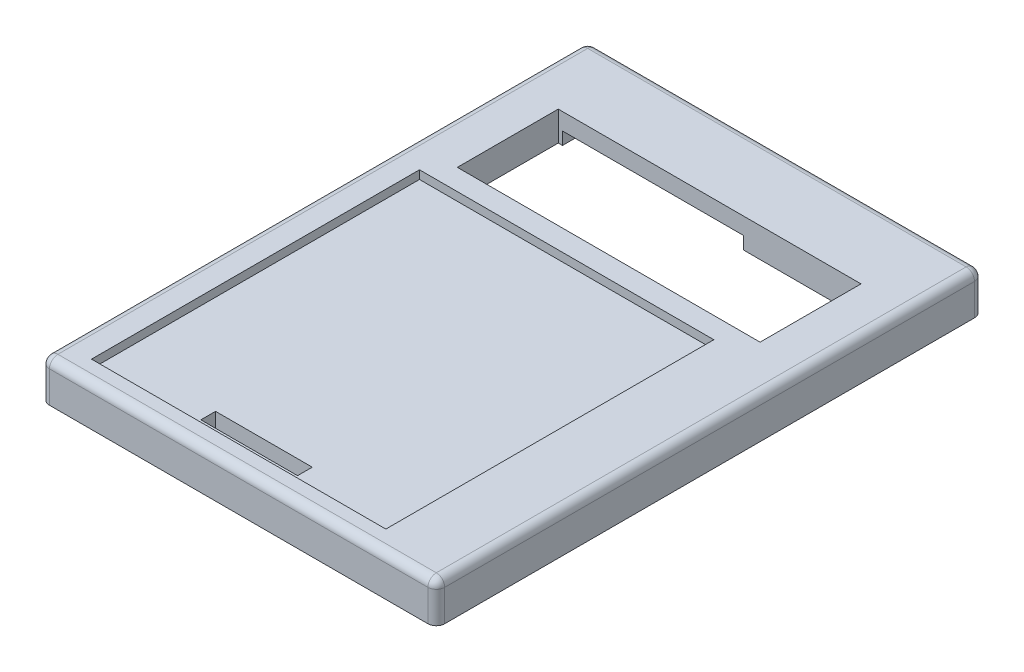
SolidWorks part; units mm, degrees
ref_plane "Front Plane" through (0, 0, 0) normal (0, 0, 1) x (1, 0, 0)
ref_plane "Top Plane" through (0, 0, 0) normal (0, 1, 0) x (1, 0, 0)
ref_plane "Right Plane" through (0, 0, 0) normal (1, 0, 0) x (0, 0, -1)
sketch "Sketch1" plane through (0, 0, 0) normal (0, 1, 0) x (1, 0, 0)
  line L1 (0, 0) -> (94, 0)
  line L2 (0, 0) -> (0, 130)
  line L3 (0, 130) -> (94, 130)
  line L4 (94, 0) -> (94, 130)
  dimension "D1" = 130
  dimension "D2" = 94
extrude "Boss-Extrude1" add sketch "Sketch1" along normal blind 7
sketch "Sketch2" plane through (0, 7, 0) normal (0, 1, 0) x (1, 0, 0)
  line L0 (94, 130) -> (0, 130) construction
  line L1 (11, 112) -> (83, 112)
  line L2 (11, 112) -> (11, 88)
  line L3 (11, 88) -> (83, 88)
  line L4 (83, 112) -> (83, 88)
  point P6 (47, 112)
  point P7 (47, 130)
  dimension "D1" = 72
  dimension "D2" = 24
  dimension "D3" = 18
extrude "Cut-Extrude1" cut sketch "Sketch2" against normal through all
sketch "Sketch3" plane through (0, 0, 0) normal (0, -1, 0) x (1, 0, 0)
  line L0 (83, -88) -> (83, -112) construction
  line L1 (89, -109) -> (83, -109)
  line L2 (89, -109) -> (89, -91)
  line L3 (89, -91) -> (83, -91)
  line L4 (83, -109) -> (83, -91)
  point P4 (83, -100)
  point P7 (83, -100)
  dimension "D1" = 6
  dimension "D2" = 18
extrude "Cut-Extrude2" cut sketch "Sketch3" against normal blind 3.5
sketch "Sketch4" plane through (0, 0, 0) normal (0, -1, 0) x (1, 0, 0)
  line L1 (55, -119.5) -> (12, -119.5)
  line L2 (55, -119.5) -> (55, -112)
  line L3 (55, -112) -> (12, -112)
  line L4 (12, -119.5) -> (12, -112)
  line L5 (83, -112) -> (11, -112) construction
  line L6 (0, -130) -> (0, 0) construction
  dimension "D1" = 43
  dimension "D2" = 7.5
  dimension "D3" = 12
extrude "Cut-Extrude3" cut sketch "Sketch4" against normal blind 3
sketch "Sketch5" plane through (0, 7, 0) normal (0, 1, 0) x (1, 0, 0)
  line L0 (0, 0) -> (94, 0) construction
  line L1 (7, 83) -> (77, 83)
  line L2 (7, 83) -> (7, 5)
  line L3 (7, 5) -> (77, 5)
  line L4 (77, 83) -> (77, 5)
  line L5 (0, 130) -> (0, 0) construction
  dimension "D1" = 78
  dimension "D2" = 70
  dimension "D3" = 5
  dimension "D4" = 7
extrude "Cut-Extrude4" cut sketch "Sketch5" against normal blind 2
sketch "Sketch6" plane through (0, 5, 0) normal (0, 1, 0) x (1, 0, 0)
  line L0 (7, 5) -> (77, 5) construction
  line L1 (30.5, 11) -> (53.5, 11)
  line L2 (30.5, 11) -> (30.5, 7.5)
  line L3 (30.5, 7.5) -> (53.5, 7.5)
  line L4 (53.5, 11) -> (53.5, 7.5)
  point P6 (42, 7.5)
  point P7 (42, 5)
  dimension "D1" = 23
  dimension "D2" = 3.5
  dimension "D3" = 2.5
extrude "Cut-Extrude5" cut sketch "Sketch6" against normal through all
fillet "Fillet1" radius 2 8 edges at (94, 3.5, -130) (0, 3.5, -130) (0, 3.5, 0) (94, 3.5, 0) (47, 7, 0) (94, 7, -65) (47, 7, -130) (0, 7, -65)
sketch "Sketch8" plane through (0, 0, 0) normal (0, -1, 0) x (1, 0, 0)
  line L0 (92, -130) -> (2, -130) construction
  line L1 (92.25, -128.25) -> (1.75, -128.25)
  line L2 (92.25, -128.25) -> (92.25, -1.75)
  line L3 (92.25, -1.75) -> (1.75, -1.75)
  line L4 (1.75, -128.25) -> (1.75, -1.75)
  line L5 (0, -128) -> (0, -2) construction
  line L6 (2, 0) -> (92, 0) construction
  line L7 (94, -2) -> (94, -128) construction
  line L8 (92, -130) -> (2, -130)
  line L9 (94, -2) -> (94, -128)
  line L10 (2, 0) -> (92, 0)
  line L11 (0, -128) -> (0, -2)
  arc A0 (0, -128) -> (2, -130) centre (2, -128) ccw construction
  arc A1 (92, -130) -> (94, -128) centre (92, -128) ccw construction
  arc A2 (94, -2) -> (92, 0) centre (92, -2) ccw construction
  arc A3 (2, 0) -> (0, -2) centre (2, -2) ccw construction
  arc A4 (0, -128) -> (2, -130) centre (2, -128) ccw
  arc A5 (92, -130) -> (94, -128) centre (92, -128) ccw
  arc A6 (94, -2) -> (92, 0) centre (92, -2) ccw
  arc A7 (2, 0) -> (0, -2) centre (2, -2) ccw
  dimension "D1" = 1.75
  dimension "D2" = 1.75
  dimension "D3" = 1.75
  dimension "D4" = 1.75
extrude "Boss-Extrude2" add sketch "Sketch8" along normal blind 2.5
sketch "Sketch9" plane through (0, 7, 0) normal (0, 1, 0) x (1, 0, 0)
  line L0 (11, 112) -> (11, 88) construction
  line L1 (11, 125.7621) -> (83, 125.7621)
  line L2 (11, 125.7621) -> (11, 116.0711)
  line L3 (11, 116.0711) -> (83, 116.0711)
  line L4 (83, 125.7621) -> (83, 116.0711)
  line L5 (83, 88) -> (83, 112) construction
  line L6 (27.9317, 125.7621) -> (21.7392, 125.7621)
  line L7 (21.7392, 125.7621) -> (21.7392, 116.0711)
  line L8 (21.7392, 116.0711) -> (27.9317, 116.0711)
  line L9 (27.9317, 116.0711) -> (27.9317, 121.976)
  line L10 (27.9317, 121.976) -> (23.7821, 121.976)
  line L11 (23.7821, 121.976) -> (23.7821, 120.2523)
  line L12 (23.7821, 120.2523) -> (26.7825, 120.9166)
  line L13 (26.7825, 120.9166) -> (26.7825, 117.7626)
  line L14 (26.7825, 117.7626) -> (22.6968, 117.7626)
  line L15 (22.6968, 117.7626) -> (22.6968, 124.1466)
  line L16 (22.6968, 124.1466) -> (27.9317, 124.1466)
  line L17 (27.9317, 124.1466) -> (27.9317, 125.7621)
  line L18 (29.5915, 125.7621) -> (29.5915, 116.0711)
  line L19 (29.5915, 116.0711) -> (30.7406, 116.0711)
  line L20 (30.7406, 116.0711) -> (30.7406, 119.2309)
  line L21 (30.7406, 119.2309) -> (33.9004, 116.0711)
  line L22 (33.9004, 116.0711) -> (35.784, 116.0711)
  line L23 (35.784, 116.0711) -> (32.6242, 119.2309)
  line L24 (32.6242, 119.2309) -> (34.2041, 119.2309)
  line L25 (34.2041, 119.2309) -> (34.2041, 125.7621)
  line L26 (34.2041, 125.7621) -> (29.5915, 125.7621)
